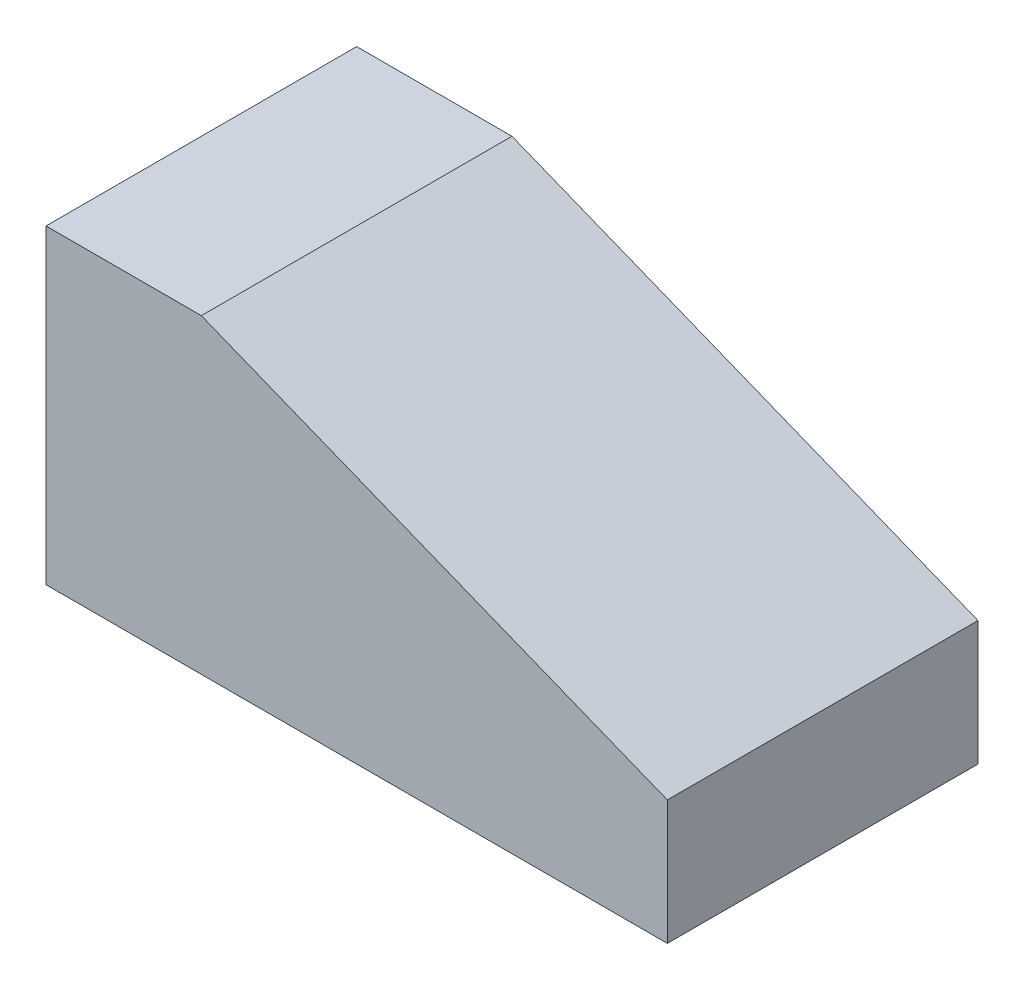
SolidWorks part; units mm, degrees
ref_plane "Front Plane" through (0, 0, 0) normal (0, 0, 1) x (1, 0, 0)
ref_plane "Top Plane" through (0, 0, 0) normal (0, 1, 0) x (1, 0, 0)
ref_plane "Right Plane" through (0, 0, 0) normal (1, 0, 0) x (0, 0, -1)
sketch "Sketch1" plane through (0, 0, 0) normal (0, 0, 1) x (1, 0, 0)
  line L0 (0, 0) -> (0, 50)
  line L1 (0, 50) -> (25, 50)
  line L2 (25, 50) -> (100, 20)
  line L3 (100, 20) -> (100, 0)
  line L4 (100, 0) -> (0, 0)
  dimension "D1" = 25
  dimension "D2" = 50
  dimension "D3" = 20
  dimension "D4" = 100
extrude "Boss-Extrude1" add sketch "Sketch1" along normal blind 50
